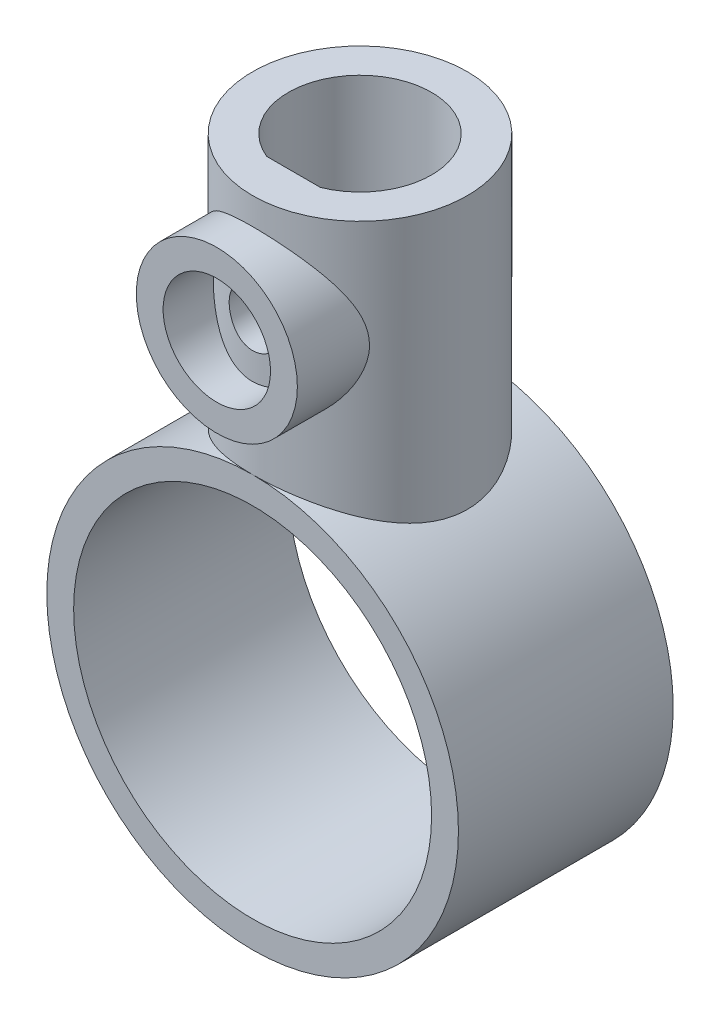
SolidWorks part; units mm, degrees
ref_plane "Front Plane" through (0, 0, 0) normal (0, 0, 1) x (1, 0, 0)
ref_plane "Top Plane" through (0, 0, 0) normal (0, 1, 0) x (1, 0, 0)
ref_plane "Right Plane" through (0, 0, 0) normal (1, 0, 0) x (0, 0, -1)
sketch "Sketch1" plane through (0, 0, 0) normal (0, 0, 1) x (1, 0, 0)
  circle A0 centre (0, 0) radius 10
  circle A1 centre (0, 0) radius 11.5
  point P5 (0.5565, 0)
  dimension "D1" = 20
  dimension "D2" = 23
extrude "Boss-Extrude1" add sketch "Sketch1" along normal mid plane 12
ref_plane "Plane1" through (0, 25, 0) normal (0, 1, 0) x (1, 0, 0)
sketch "Sketch2" plane through (0, 25, 0) normal (0, 1, 0) x (1, 0, 0)
  circle A0 centre (0, 0) radius 6
  point P3 (0, 0)
  dimension "D1" = 12
extrude "Boss-Extrude3" add sketch "Sketch2" against normal blind 18
sketch "Sketch4" plane through (0, 0, 0) normal (0, 0, 1) x (1, 0, 0)
  circle A0 centre (0, 0) radius 10
extrude "Cut-Extrude2" cut sketch "Sketch4" against normal through all both and the other way through all
sketch "Sketch5" plane through (0, 25, 0) normal (0, 1, 0) x (1, 0, 0)
  circle A0 centre (0, 0) radius 4
  dimension "D1" = 8
extrude "Cut-Extrude3" cut sketch "Sketch5" against normal blind 10
ref_plane "Plane2" through (0, 0, 8) normal (0, 0, 1) x (1, 0, 0)
sketch "Sketch6" plane through (0, 0, 8) normal (0, 0, 1) x (1, 0, 0)
  line L0 (6.6, 25) -> (-6.6, 25) construction
  circle A0 centre (0, 19) radius 4.5
  circle A1 centre (0, 19) radius 3
  dimension "D2" = 9
  dimension "D3" = 6
  dimension "D1" = 6
extrude "Boss-Extrude4" add sketch "Sketch6" against normal blind 5
sketch "Sketch7" plane through (0, 25, 0) normal (0, 1, 0) x (1, 0, 0)
  circle A0 centre (0, 0) radius 4
extrude "Cut-Extrude4" cut sketch "Sketch7" against normal blind 10
sketch "Sketch8" plane through (0, 25, 0) normal (0, 1, 0) x (1, 0, 0)
  line L0 (-1.5, -3.7081) -> (1.5, -3.7081)
  circle A0 centre (0, 0) radius 4 construction
  arc A1 (-1.5, -3.7081) -> (1.5, -3.7081) centre (0, 0) ccw
  point P4 (0, -3.7081)
  dimension "D1" = 3
extrude "Boss-Extrude5" add sketch "Sketch8" against normal blind 21
sketch "Sketch9" plane through (0, 0, 8) normal (0, 0, 1) x (1, 0, 0)
  circle A0 centre (0, 0) radius 10
extrude "Cut-Extrude5" cut sketch "Sketch9" against normal through all both and the other way through all
sketch "Sketch10" plane through (0, 0, 8) normal (0, 0, 1) x (1, 0, 0)
  circle A0 centre (0, 19) radius 1.5
  dimension "D1" = 3
extrude "Cut-Extrude6" cut sketch "Sketch10" against normal blind 8
